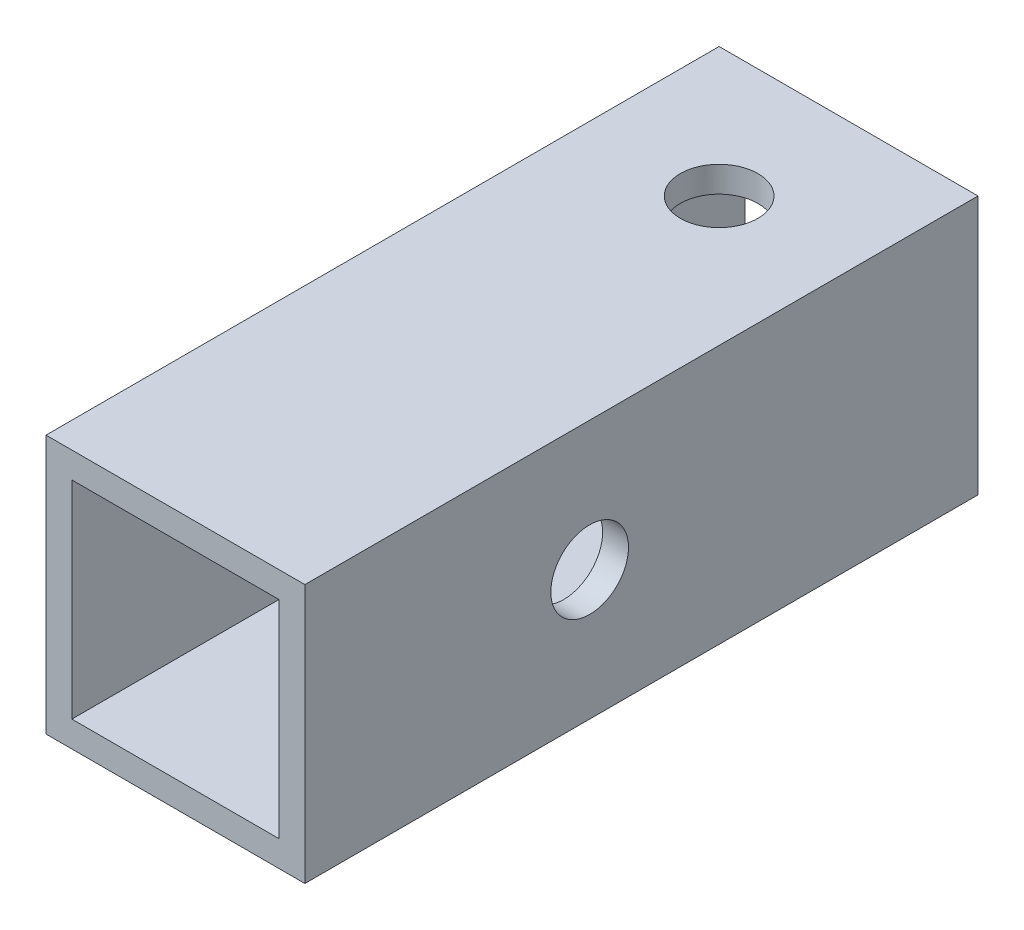
SolidWorks part; units mm, degrees
material "6063-O"
ref_plane "前视基准面" through (0, 0, 0) normal (0, 0, 1) x (1, 0, 0)
ref_plane "上视基准面" through (0, 0, 0) normal (0, 1, 0) x (1, 0, 0)
ref_plane "右视基准面" through (0, 0, 0) normal (1, 0, 0) x (0, 0, -1)
other "Configuration Table"
sketch "草图1" plane through (0, 0, 0) normal (0, 0, 1) x (1, 0, 0)
  line L1 (-5, 5) -> (5, 5)
  line L2 (-5, 5) -> (-5, -5)
  line L3 (-5, -5) -> (5, -5)
  line L4 (5, 5) -> (5, -5)
  line L5 (-5, 5) -> (5, -5) construction
  line L6 (-5, -5) -> (5, 5) construction
  point P4 (0, 0)
  dimension "D1" = 10
  dimension "D2" = 10
extrude "拉伸-薄壁1" add sketch "草图1" along normal blind 26 thin
sketch "草图2" plane through (0, 5, 0) normal (0, 1, 0) x (1, 0, 0)
  line L6 (0, 0) -> (0, -38) construction
  line L7 (5, 0) -> (-5, 0) construction
  circle A0 centre (0, -5) radius 1.5
  circle A1 centre (0, -20) radius 1.5 construction
  dimension "D2" = 3
  dimension "D4" = 15
  dimension "D3" = 5
extrude "切除-拉伸1" cut sketch "草图2" against normal blind 50
sketch "草图3" plane through (5, 0, 0) normal (1, 0, 0) x (0, 0, -1)
  line L0 (0, 0) -> (-44.741, 0) construction
  line L1 (0, -5) -> (0, 5) construction
  circle A0 centre (-15, 0) radius 1.5
  circle A1 centre (-30, 0) radius 1.5 construction
  dimension "D1" = 15
  dimension "D2" = 15
  dimension "D3" = 3
extrude "切除-拉伸2" cut sketch "草图3" against normal blind 10
